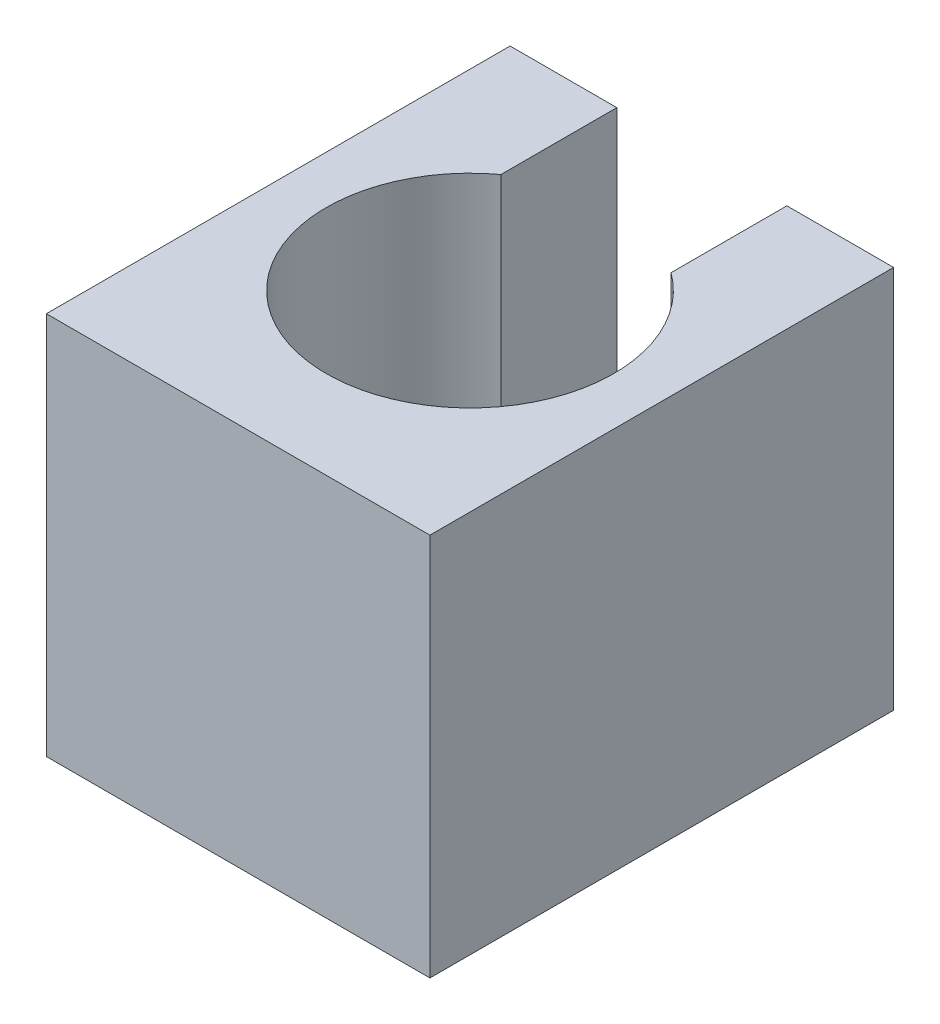
SolidWorks part; units mm, degrees
ref_plane "Спереди" through (0, 0, 0) normal (0, 0, 1) x (1, 0, 0)
ref_plane "Сверху" through (0, 0, 0) normal (0, 1, 0) x (1, 0, 0)
ref_plane "Справа" through (0, 0, 0) normal (1, 0, 0) x (0, 0, -1)
sketch "Эскиз1" plane through (0, 0, 0) normal (0, 1, 0) x (1, 0, 0)
  line L0 (0, 3.627) -> (0, -3.627) construction
  line L1 (-3, 3.627) -> (-1.3303, 3.627)
  line L2 (-3, 3.627) -> (-3, -3.627)
  line L3 (-3, -3.627) -> (3, -3.627)
  line L4 (3, 3.627) -> (3, -3.627)
  line L5 (-3, 3.627) -> (3, -3.627) construction
  line L6 (-3, -3.627) -> (3, 3.627) construction
  line L7 (-1.3303, 3.627) -> (-1.3303, 1.8146)
  line L8 (1.3303, 3.627) -> (1.3303, 1.8146)
  line L9 (1.3303, 3.627) -> (3, 3.627)
  arc A0 (-1.3303, 1.8146) -> (1.3303, 1.8146) centre (0, 0) ccw
  dimension "D1" = 4.5
  dimension "D2" = 6
extrude "Бобышка-Вытянуть1" add sketch "Эскиз1" along normal blind 6
